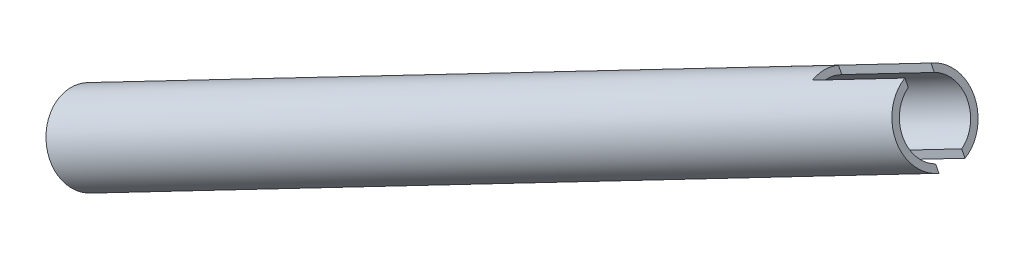
SolidWorks part; units mm, degrees
ref_plane "Front" through (0, 0, 0) normal (0, 0, 1) x (1, 0, 0)
ref_plane "Top" through (0, 0, 0) normal (0, 1, 0) x (1, 0, 0)
ref_plane "Right" through (0, 0, 0) normal (1, 0, 0) x (0, 0, -1)
sketch "Sketch1" plane through (0, 0, 0) normal (0, 0, 1) x (1, 0, 0)
  line L0 (319.107, -1704.49) -> (525.0288, -1597.3769) construction
  line L1 (581.3633, -1568.0737) -> (275.4478, -1727.2) construction
  line L2 (525.0288, -1597.3769) -> (528.6624, -1604.3623) construction
  line L3 (528.6624, -1604.3623) -> (529.4243, -1605.827)
  line L4 (529.4243, -1605.827) -> (323.5025, -1712.9402)
  line L5 (323.5025, -1712.9402) -> (322.7406, -1711.4755)
  line L6 (322.7406, -1711.4755) -> (528.6624, -1604.3623)
  line L7 (319.107, -1704.49) -> (322.7406, -1711.4755) construction
  dimension "D1" = 1.651
  dimension "D2" = 9.525
revolve "Revolve1" add sketch "Sketch1" angle 360 about L0
sketch "Sketch2" plane through (-240.7342, -125.2214, 0) normal (0.8872, 0.4615, 0) x (0, 0, -1)
  line L0 (-3.175, -1634.6706) -> (-3.175, -1629.0372) construction
  line L1 (-3.175, -1649.8829) -> (3.175, -1649.8829)
  line L2 (-3.175, -1649.8829) -> (-3.175, -1668.9329)
  line L3 (-3.175, -1668.9329) -> (3.175, -1668.9329)
  line L4 (3.175, -1649.8829) -> (3.175, -1668.9329)
  line L5 (3.175, -1628.81) -> (3.175, -1634.6706) construction
  circle A0 centre (0, -1659.4079) radius 9.525 construction
  point P4 (0, -1668.9329)
  point P7 (0, -1649.8829)
extrude "Cut-Extrude1" cut sketch "Sketch2" against normal up to surface (25.4 mm away)
equation "\"D1@Sketch1\"=\"a arm tube thickness@FS2-SU-FS-A-0002-V1, FRONT LEFT SUSPENSION.SLDASM\""
equation "\"D2@Sketch1\"=\"a arm tube diameter@FS2-SU-FS-A-0002-V1, FRONT LEFT SUSPENSION.SLDASM\"/2"
